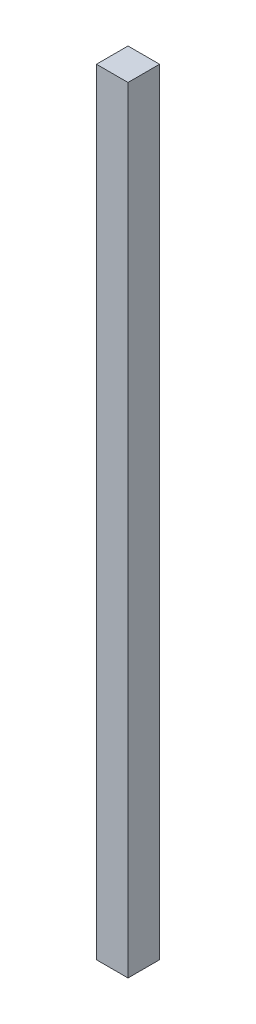
SolidWorks part; units mm, degrees
ref_plane "Plan de face" through (0, 0, 0) normal (0, 0, 1) x (1, 0, 0)
ref_plane "Plan de dessus" through (0, 0, 0) normal (0, 1, 0) x (1, 0, 0)
ref_plane "Plan de droite" through (0, 0, 0) normal (1, 0, 0) x (0, 0, -1)
sketch "Esquisse1" plane through (0, 0, 0) normal (0, 1, 0) x (1, 0, 0)
  line L1 (-5.7, 5.7) -> (5.7, 5.7)
  line L2 (-5.7, 5.7) -> (-5.7, -5.7)
  line L3 (-5.7, -5.7) -> (5.7, -5.7)
  line L4 (5.7, 5.7) -> (5.7, -5.7)
  line L5 (-5.7, 5.7) -> (5.7, -5.7) construction
  line L6 (-5.7, -5.7) -> (5.7, 5.7) construction
  point P0 (0, 0)
  dimension "D1" = 11.4
  dimension "D2" = 11.4
extrude "Boss.-Extru.1" add sketch "Esquisse1" along normal blind 280
